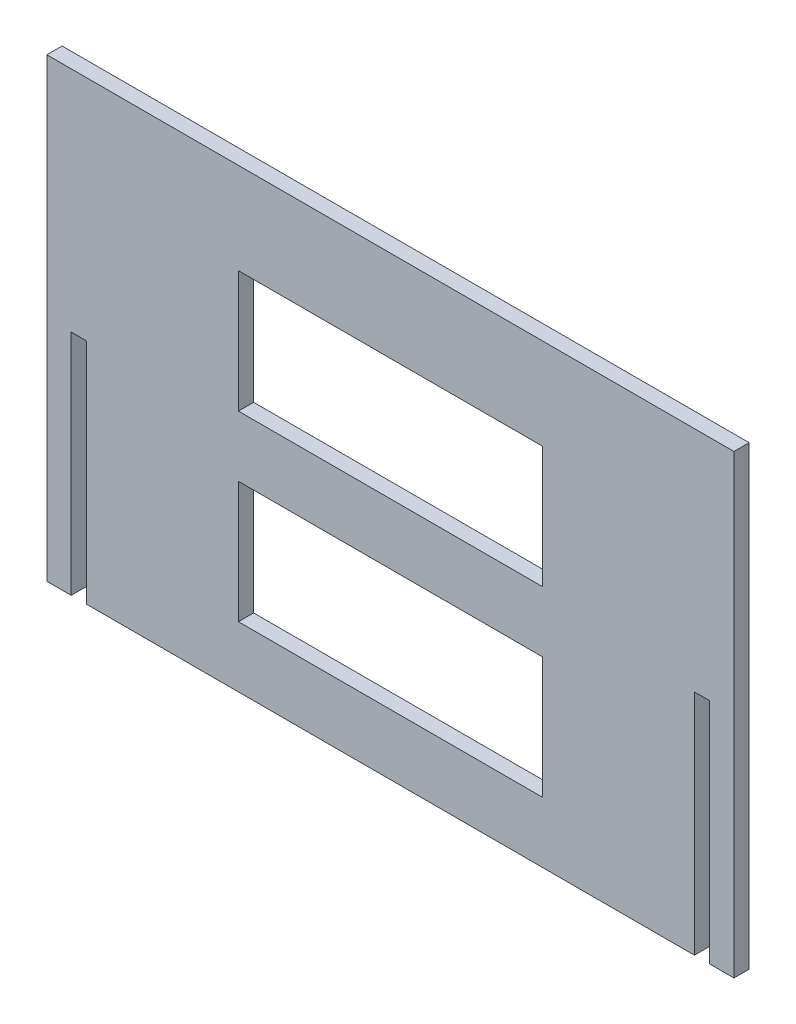
SolidWorks part; units mm, degrees
ref_plane "Plan de face" through (0, 0, 0) normal (0, 0, 1) x (1, 0, 0)
ref_plane "Plan de dessus" through (0, 0, 0) normal (0, 1, 0) x (1, 0, 0)
ref_plane "Plan de droite" through (0, 0, 0) normal (1, 0, 0) x (0, 0, -1)
sketch "Esquisse1" plane through (0, 0, 0) normal (0, 0, 1) x (1, 0, 0)
  line L0 (-8, 0) -> (0, 0)
  line L1 (0, 0) -> (0, 75)
  line L2 (0, 75) -> (5, 75)
  line L3 (5, 75) -> (5, 0)
  line L4 (5, 0) -> (205, 0)
  line L5 (205, 0) -> (205, 75)
  line L6 (205, 75) -> (210, 75)
  line L7 (210, 75) -> (210, 0)
  line L8 (210, 0) -> (218, 0)
  line L9 (218, 0) -> (218, 150)
  line L10 (218, 150) -> (-8, 150)
  line L11 (-8, 150) -> (-8, 0)
  line L13 (55, 60) -> (155, 60)
  line L14 (55, 60) -> (55, 20)
  line L15 (55, 20) -> (155, 20)
  line L16 (155, 60) -> (155, 20)
  line L17 (55, 120) -> (155, 120)
  line L18 (55, 120) -> (55, 80)
  line L19 (55, 80) -> (155, 80)
  line L20 (155, 120) -> (155, 80)
  point P21 (155, 40)
  dimension "D1" = 200
  dimension "D2" = 5
  dimension "D3" = 5
  dimension "D4" = 8
  dimension "D5" = 8
  dimension "D6" = 150
  dimension "D7" = 75
  dimension "D8" = 75
  dimension "D9" = 40
  dimension "D10" = 40
  dimension "D11" = 100
  dimension "D12" = 100
  dimension "D13" = 50
  dimension "D14" = 20
  dimension "D15" = 30
extrude "Boss.-Extru.1" add sketch "Esquisse1" along normal blind 5
